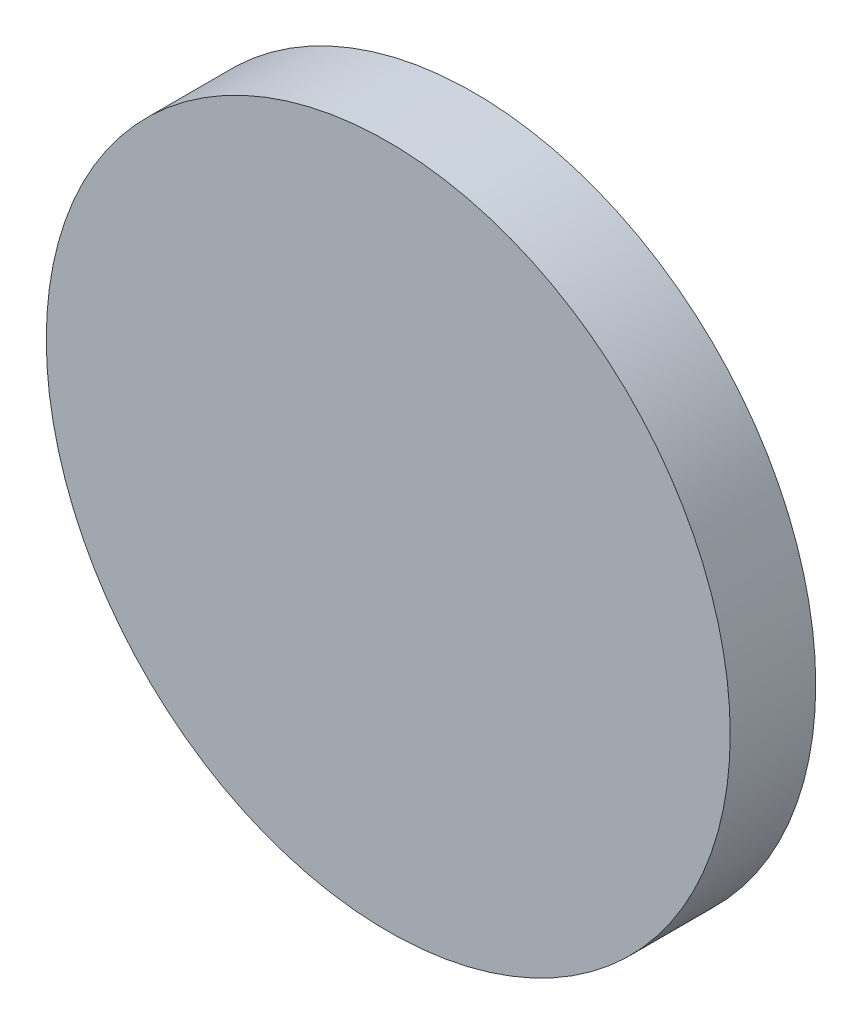
SolidWorks part; units mm, degrees
ref_plane "Front Plane" through (0, 0, 0) normal (0, 0, 1) x (1, 0, 0)
ref_plane "Top Plane" through (0, 0, 0) normal (0, 1, 0) x (1, 0, 0)
ref_plane "Right Plane" through (0, 0, 0) normal (1, 0, 0) x (0, 0, -1)
sketch "Sketch1" plane through (0, 0, 0) normal (0, 0, 1) x (1, 0, 0)
  circle A0 centre (0, 0) radius 4
  dimension "D1" = 8
extrude "Boss-Extrude1" add sketch "Sketch1" along normal blind 1
